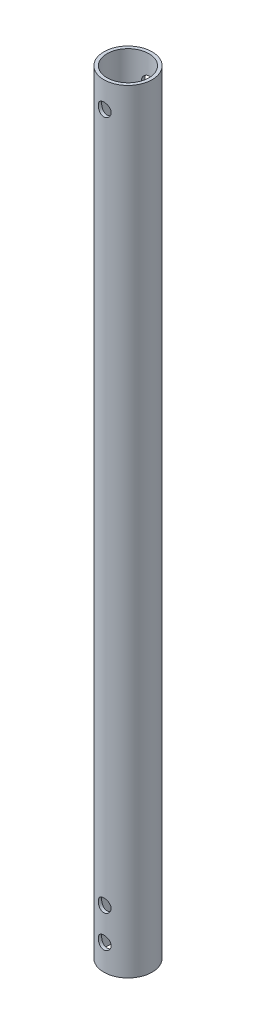
SolidWorks part; units mm, degrees
material "Carbon Fibre"
ref_plane "Front Plane" through (0, 0, 0) normal (0, 0, 1) x (1, 0, 0)
ref_plane "Top Plane" through (0, 0, 0) normal (0, 1, 0) x (1, 0, 0)
ref_plane "Right Plane" through (0, 0, 0) normal (1, 0, 0) x (0, 0, -1)
sketch "Sketch1" plane through (0, 0, 0) normal (0, 1, 0) x (1, 0, 0)
  circle A0 centre (0, 0) radius 7.5
  circle A1 centre (0, 0) radius 6.5
  dimension "D1" = 15
  dimension "D2" = 13
extrude "Boss-Extrude1" add sketch "Sketch1" along normal blind 240
sketch "Sketch2" plane through (0, 0, 0) normal (0, 0, 1) x (1, 0, 0)
  line L0 (-7.5, 0) -> (7.5, 0) construction
  line L1 (7.5, 240) -> (-7.5, 240) construction
  circle A0 centre (0, 8) radius 2
  circle A1 centre (0, 18) radius 2
  circle A2 centre (0, 242) radius 2
  circle A3 centre (0, 232) radius 2
  dimension "D1" = 4
  dimension "D3" = 8
  dimension "D5" = 8
  dimension "D2" = 10
  dimension "D4" = 10
extrude "Cut-Extrude1" cut sketch "Sketch2" against normal mid plane 18
equation "\"D1@Boss-Extrude1\"=0.6*400.00mm"
